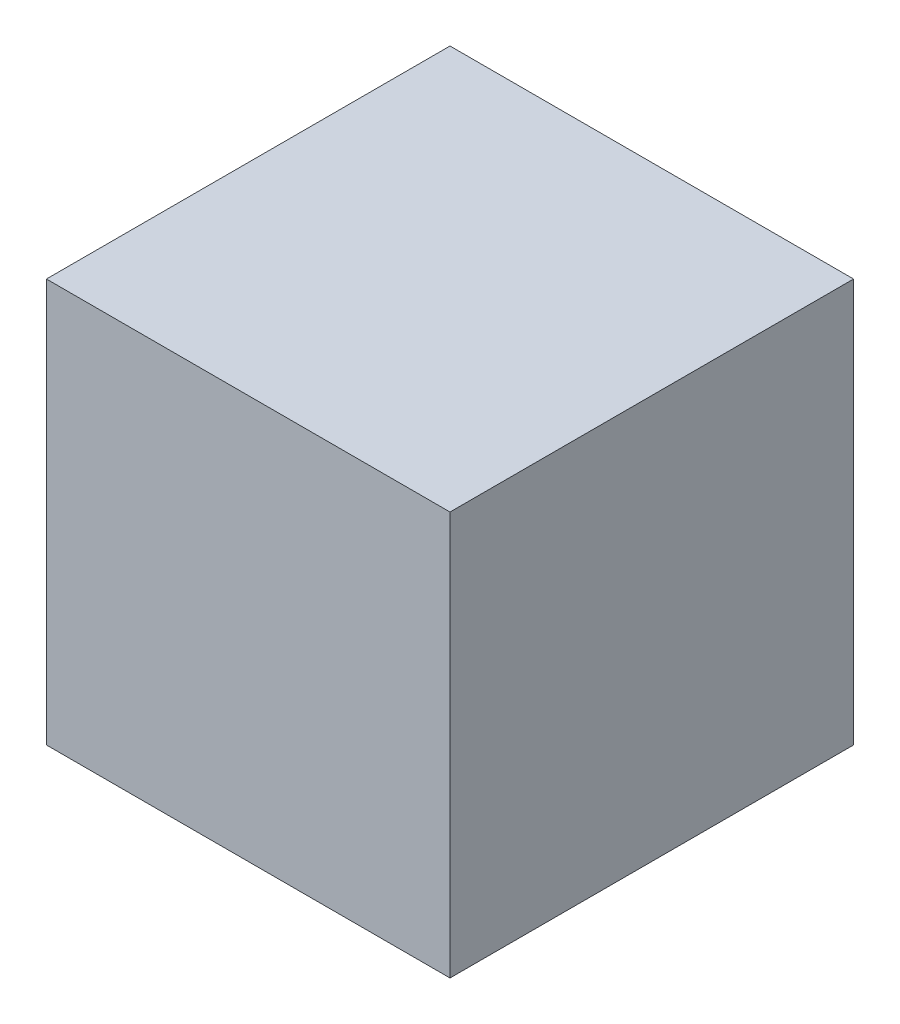
SolidWorks part; units mm, degrees
ref_plane "Front Plane" through (0, 0, 0) normal (0, 0, 1) x (1, 0, 0)
ref_plane "Top Plane" through (0, 0, 0) normal (0, 1, 0) x (1, 0, 0)
ref_plane "Right Plane" through (0, 0, 0) normal (1, 0, 0) x (0, 0, -1)
sketch "Sketch1" plane through (0, 0, 0) normal (0, 1, 0) x (1, 0, 0)
  line L1 (0, 0) -> (-10, 0)
  line L2 (0, 0) -> (0, 10)
  line L3 (0, 10) -> (-10, 10)
  line L4 (-10, 0) -> (-10, 10)
  dimension "D1" = 10
  dimension "D2" = 10
extrude "Boss-Extrude2" add sketch "Sketch1" along normal blind 10 contours L3 L4 L1 L2
